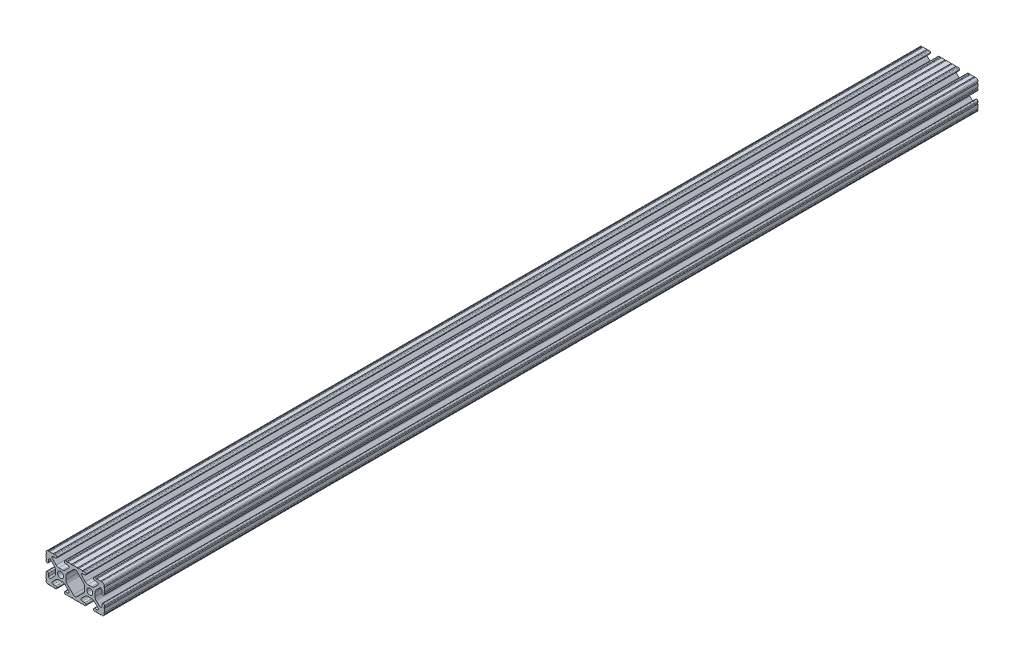
SolidWorks part; units mm, degrees
material "6061 Alloy"
ref_plane "Front Plane" through (0, 0, 0) normal (0, 0, 1) x (1, 0, 0)
ref_plane "Top Plane" through (0, 0, 0) normal (0, 1, 0) x (1, 0, 0)
ref_plane "Right Plane" through (0, 0, 0) normal (1, 0, 0) x (0, 0, -1)
sketch "Sketch1" plane through (0, 0, 0) normal (0, 0, 1) x (1, 0, 0)
  line L0 (-32.9707, 0) -> (32.2708, 0) construction
  line L1 (0, 12.7) -> (0, 0) construction
  line L2 (-12.7, 14.992) -> (-12.7, -12.6999) construction
  line L3 (12.7, 13.9801) -> (12.7, -13.3809) construction
  line L4 (-7.2595, -3.8694) -> (-1.5457, -9.5728)
  line L5 (1.5457, -9.5728) -> (7.2595, -3.8694)
  line L7 (-0.3952, 10.033) -> (0.5515, 10.033)
  line L9 (0.4332, -10.033) -> (-0.4332, -10.033)
  line L12 (8.1915, -1.6223) -> (8.1915, 1.6223)
  line L13 (7.2829, 3.8459) -> (1.6756, 9.5611)
  line L14 (-1.504, 9.5765) -> (-7.252, 3.8768)
  line L15 (-8.1915, 1.6223) -> (-8.1915, -1.6223)
  line L16 (22.2504, 12.7) -> (19.0331, 12.7)
  line L17 (18.0171, 12.7) -> (16.9875, 12.7)
  line L18 (15.9385, 11.651) -> (15.9385, 11.5392)
  line L19 (16.9875, 10.4902) -> (19.1164, 10.4902)
  line L20 (19.8441, 8.7652) -> (16.619, 5.4551)
  line L21 (14.3449, 4.4958) -> (11.0833, 4.4958)
  line L22 (8.817, 5.4472) -> (5.5642, 8.7627)
  line L23 (6.2894, 10.4902) -> (8.4125, 10.4902)
  line L24 (9.4615, 11.5392) -> (9.4615, 11.651)
  line L25 (8.4125, 12.7) -> (7.3829, 12.7)
  line L26 (6.3669, 12.7) -> (3.1496, 12.7)
  line L27 (2.1336, 12.7) -> (-2.1336, 12.7)
  line L28 (-3.1496, 12.7) -> (-6.3669, 12.7)
  line L29 (-7.3829, 12.7) -> (-8.4125, 12.7)
  line L30 (-9.4615, 11.651) -> (-9.4615, 11.5392)
  line L31 (-8.4125, 10.4902) -> (-6.2836, 10.4902)
  line L32 (-5.5326, 8.6661) -> (-8.81, 5.4163)
  line L33 (-11.0455, 4.4958) -> (-14.3545, 4.4958)
  line L34 (-16.59, 5.4163) -> (-19.8674, 8.6661)
  line L35 (-19.1164, 10.4902) -> (-16.9875, 10.4902)
  line L36 (-15.9385, 11.5392) -> (-15.9385, 11.651)
  line L37 (-16.9875, 12.7) -> (-18.0171, 12.7)
  line L38 (-19.0331, 12.7) -> (-22.2504, 12.7)
  line L39 (-25.4, 9.5504) -> (-25.4, 6.3331)
  line L40 (-25.4, 5.3171) -> (-25.4, 4.2375)
  line L41 (-24.401, 3.2385) -> (-24.2392, 3.2385)
  line L42 (-23.1902, 4.2875) -> (-23.1902, 6.3347)
  line L43 (-21.434, 7.0665) -> (-18.148, 3.8082)
  line L44 (-17.2085, 1.5536) -> (-17.2085, -1.6952)
  line L45 (-18.1405, -3.9423) -> (-21.4316, -7.2274)
  line L46 (-23.1902, -6.498) -> (-23.1902, -4.2875)
  line L47 (-24.2392, -3.2385) -> (-24.351, -3.2385)
  line L48 (-25.4, -4.2875) -> (-25.4, -5.3171)
  line L49 (-25.4, -6.3331) -> (-25.4, -9.5504)
  line L50 (-22.2504, -12.7) -> (-19.0331, -12.7)
  line L51 (-18.0171, -12.7) -> (-16.9875, -12.7)
  line L52 (-15.9384, -11.651) -> (-15.9384, -11.5392)
  line L53 (-16.9875, -10.4902) -> (-19.1164, -10.4902)
  line L54 (-19.8341, -8.7551) -> (-16.4966, -5.4237)
  line L55 (-14.2536, -4.4958) -> (-11.1464, -4.4958)
  line L56 (-8.9034, -5.4237) -> (-5.5659, -8.7551)
  line L57 (-6.2836, -10.4902) -> (-8.4125, -10.4902)
  line L58 (-9.4616, -11.5392) -> (-9.4616, -11.651)
  line L59 (-8.4125, -12.7) -> (-7.3829, -12.7)
  line L60 (-6.3669, -12.7) -> (-3.1496, -12.7)
  line L61 (-2.1336, -12.7) -> (2.1336, -12.7)
  line L62 (3.1496, -12.7) -> (6.3669, -12.7)
  line L63 (7.3829, -12.7) -> (8.4125, -12.7)
  line L64 (9.4616, -11.651) -> (9.4616, -11.5392)
  line L65 (8.4125, -10.4902) -> (6.2894, -10.4902)
  line L66 (5.4807, -8.5353) -> (8.5979, -5.4237)
  line L67 (10.8409, -4.4958) -> (14.1026, -4.4958)
  line L68 (16.1879, -5.2766) -> (19.8682, -8.4822)
  line L69 (19.1164, -10.4902) -> (16.9875, -10.4902)
  line L70 (15.9384, -11.5392) -> (15.9384, -11.651)
  line L71 (16.9875, -12.7) -> (18.0171, -12.7)
  line L72 (19.0331, -12.7) -> (22.2504, -12.7)
  line L73 (25.4, -9.5504) -> (25.4, -6.3331)
  line L74 (25.4, -5.3171) -> (25.4, -4.2375)
  line L75 (24.401, -3.2385) -> (24.1892, -3.2385)
  line L76 (23.1902, -4.2375) -> (23.1902, -6.1559)
  line L77 (21.584, -6.8869) -> (18.2982, -4.025)
  line L78 (17.2085, -1.6308) -> (17.2085, 1.6308)
  line L79 (18.1094, 3.8465) -> (21.5263, 7.3534)
  line L80 (23.1902, 6.6769) -> (23.1902, 4.2375)
  line L81 (24.1892, 3.2385) -> (24.401, 3.2385)
  line L82 (25.4, 4.2375) -> (25.4, 5.3171)
  line L83 (25.4, 6.3332) -> (25.4, 9.5504)
  circle A0 centre (-12.7, 0) radius 2.6035
  circle A1 centre (12.7, 0) radius 2.6035
  arc A2 (-0.3952, 10.033) -> (-1.504, 9.5765) centre (-0.3952, 8.4582) ccw
  arc A3 (0.5515, 10.033) -> (1.6756, 9.5611) centre (0.5515, 8.4582) cw
  arc A4 (-8.1915, -1.6223) -> (-7.2595, -3.8694) centre (-5.0165, -1.6223) ccw
  arc A5 (-0.4332, -10.033) -> (-1.5457, -9.5728) centre (-0.4332, -8.4582) cw
  arc A6 (7.2595, -3.8694) -> (8.1915, -1.6223) centre (5.0165, -1.6223) ccw
  arc A7 (8.1915, 1.6223) -> (7.2829, 3.8459) centre (5.0165, 1.6223) ccw
  arc A8 (0.4332, -10.033) -> (1.5457, -9.5728) centre (0.4332, -8.4582) ccw
  arc A9 (-7.252, 3.8768) -> (-8.1915, 1.6223) centre (-5.0165, 1.6223) ccw
  arc A16 (25.3998, 10.5664) -> (23.2664, 12.6998) centre (23.2918, 10.5918) ccw
  arc A17 (22.2504, 12.7) -> (23.2664, 12.6998) centre (22.7584, 12.7) ccw
  arc A18 (18.0171, 12.7) -> (19.0331, 12.7) centre (18.5251, 12.7) ccw
  arc A19 (16.9875, 12.7) -> (15.9385, 11.651) centre (16.9875, 11.651) ccw
  arc A20 (15.9385, 11.5392) -> (16.9875, 10.4902) centre (16.9875, 11.5392) ccw
  arc A21 (19.8441, 8.7652) -> (19.1164, 10.4902) centre (19.1164, 9.4742) ccw
  arc A22 (14.3449, 4.4958) -> (16.619, 5.4551) centre (14.3449, 7.6708) ccw
  arc A23 (8.817, 5.4472) -> (11.0833, 4.4958) centre (11.0833, 7.6708) ccw
  arc A24 (6.2894, 10.4902) -> (5.5642, 8.7627) centre (6.2894, 9.4742) ccw
  arc A25 (8.4125, 10.4902) -> (9.4615, 11.5392) centre (8.4125, 11.5392) ccw
  arc A26 (9.4615, 11.651) -> (8.4125, 12.7) centre (8.4125, 11.651) ccw
  arc A27 (6.3669, 12.7) -> (7.3829, 12.7) centre (6.8749, 12.7) ccw
  arc A28 (2.1336, 12.7) -> (3.1496, 12.7) centre (2.6416, 12.7) ccw
  arc A29 (-3.1496, 12.7) -> (-2.1336, 12.7) centre (-2.6416, 12.7) ccw
  arc A30 (-7.3829, 12.7) -> (-6.3669, 12.7) centre (-6.8749, 12.7) ccw
  arc A31 (-8.4125, 12.7) -> (-9.4615, 11.651) centre (-8.4125, 11.651) ccw
  arc A32 (-9.4615, 11.5392) -> (-8.4125, 10.4902) centre (-8.4125, 11.5392) ccw
  arc A33 (-5.5326, 8.6661) -> (-6.2836, 10.4902) centre (-6.2836, 9.4235) ccw
  arc A34 (-11.0455, 4.4958) -> (-8.81, 5.4163) centre (-11.0455, 7.6708) ccw
  arc A35 (-16.59, 5.4163) -> (-14.3545, 4.4958) centre (-14.3545, 7.6708) ccw
  arc A36 (-19.1164, 10.4902) -> (-19.8674, 8.6661) centre (-19.1164, 9.4235) ccw
  arc A37 (-16.9875, 10.4902) -> (-15.9385, 11.5392) centre (-16.9875, 11.5392) ccw
  arc A38 (-15.9385, 11.651) -> (-16.9875, 12.7) centre (-16.9875, 11.651) ccw
  arc A39 (-19.0331, 12.7) -> (-18.0171, 12.7) centre (-18.5251, 12.7) ccw
  arc A40 (-23.2664, 12.6998) -> (-22.2504, 12.7) centre (-22.7584, 12.7) ccw
  arc A41 (-23.2664, 12.6998) -> (-25.3998, 10.5664) centre (-23.2918, 10.5918) ccw
  arc A42 (-25.4, 9.5504) -> (-25.3998, 10.5664) centre (-25.4, 10.0584) ccw
  arc A43 (-25.4, 5.3171) -> (-25.4, 6.3331) centre (-25.4, 5.8251) ccw
  arc A44 (-25.4, 4.2375) -> (-24.401, 3.2385) centre (-24.401, 4.2375) ccw
  arc A45 (-24.2392, 3.2385) -> (-23.1902, 4.2875) centre (-24.2392, 4.2875) ccw
  arc A46 (-21.434, 7.0665) -> (-23.1902, 6.3347) centre (-22.1596, 6.3347) ccw
  arc A47 (-17.2085, 1.5536) -> (-18.148, 3.8082) centre (-20.3835, 1.5536) ccw
  arc A48 (-18.1405, -3.9423) -> (-17.2085, -1.6952) centre (-20.3835, -1.6952) ccw
  arc A49 (-23.1902, -6.498) -> (-21.4316, -7.2274) centre (-22.1596, -6.498) ccw
  arc A50 (-23.1902, -4.2875) -> (-24.2392, -3.2385) centre (-24.2392, -4.2875) ccw
  arc A51 (-24.351, -3.2385) -> (-25.4, -4.2875) centre (-24.351, -4.2875) ccw
  arc A52 (-25.4, -6.3331) -> (-25.4, -5.3171) centre (-25.4, -5.8251) ccw
  arc A53 (-25.3998, -10.5664) -> (-25.4, -9.5504) centre (-25.4, -10.0584) ccw
  arc A54 (-25.3998, -10.5664) -> (-23.2664, -12.6998) centre (-23.2918, -10.5918) ccw
  arc A55 (-22.2504, -12.7) -> (-23.2664, -12.6998) centre (-22.7584, -12.7) ccw
  arc A56 (-18.0171, -12.7) -> (-19.0331, -12.7) centre (-18.5251, -12.7) ccw
  arc A57 (-16.9875, -12.7) -> (-15.9384, -11.651) centre (-16.9875, -11.651) ccw
  arc A58 (-15.9384, -11.5392) -> (-16.9875, -10.4902) centre (-16.9875, -11.5392) ccw
  arc A59 (-19.8341, -8.7551) -> (-19.1164, -10.4902) centre (-19.1164, -9.4742) ccw
  arc A60 (-14.2536, -4.4958) -> (-16.4966, -5.4237) centre (-14.2536, -7.6708) ccw
  arc A61 (-8.9034, -5.4237) -> (-11.1464, -4.4958) centre (-11.1464, -7.6708) ccw
  arc A62 (-6.2836, -10.4902) -> (-5.5659, -8.7551) centre (-6.2836, -9.4742) ccw
  arc A63 (-8.4125, -10.4902) -> (-9.4616, -11.5392) centre (-8.4125, -11.5392) ccw
  arc A64 (-9.4616, -11.651) -> (-8.4125, -12.7) centre (-8.4125, -11.651) ccw
  arc A65 (-6.3669, -12.7) -> (-7.3829, -12.7) centre (-6.8749, -12.7) ccw
  arc A66 (-2.1336, -12.7) -> (-3.1496, -12.7) centre (-2.6416, -12.7) ccw
  arc A67 (3.1496, -12.7) -> (2.1336, -12.7) centre (2.6416, -12.7) ccw
  arc A68 (7.3829, -12.7) -> (6.3669, -12.7) centre (6.8749, -12.7) ccw
  arc A69 (8.4125, -12.7) -> (9.4616, -11.651) centre (8.4125, -11.651) ccw
  arc A70 (9.4616, -11.5392) -> (8.4125, -10.4902) centre (8.4125, -11.5392) ccw
  arc A71 (5.4807, -8.5353) -> (6.2894, -10.4902) centre (6.2894, -9.3455) ccw
  arc A72 (10.8409, -4.4958) -> (8.5979, -5.4237) centre (10.8409, -7.6708) ccw
  arc A73 (16.1879, -5.2766) -> (14.1026, -4.4958) centre (14.1026, -7.6708) ccw
  arc A74 (19.1164, -10.4902) -> (19.8682, -8.4822) centre (19.1164, -9.3455) ccw
  arc A75 (16.9875, -10.4902) -> (15.9384, -11.5392) centre (16.9875, -11.5392) ccw
  arc A76 (15.9384, -11.651) -> (16.9875, -12.7) centre (16.9875, -11.651) ccw
  arc A77 (19.0331, -12.7) -> (18.0171, -12.7) centre (18.5251, -12.7) ccw
  arc A78 (23.2664, -12.6998) -> (22.2504, -12.7) centre (22.7584, -12.7) ccw
  arc A79 (23.2664, -12.6998) -> (25.3998, -10.5664) centre (23.2918, -10.5918) ccw
  arc A80 (25.4, -9.5504) -> (25.3998, -10.5664) centre (25.4, -10.0584) ccw
  arc A81 (25.4, -5.3171) -> (25.4, -6.3331) centre (25.4, -5.8251) ccw
  arc A82 (25.4, -4.2375) -> (24.401, -3.2385) centre (24.401, -4.2375) ccw
  arc A83 (24.1892, -3.2385) -> (23.1902, -4.2375) centre (24.1892, -4.2375) ccw
  arc A84 (21.584, -6.8869) -> (23.1902, -6.1559) centre (22.2207, -6.1559) ccw
  arc A85 (17.2085, -1.6308) -> (18.2982, -4.025) centre (20.3835, -1.6308) ccw
  arc A86 (18.1094, 3.8465) -> (17.2085, 1.6308) centre (20.3835, 1.6308) ccw
  arc A87 (23.1902, 6.6769) -> (21.5263, 7.3534) centre (22.2207, 6.6769) ccw
  arc A88 (23.1902, 4.2375) -> (24.1892, 3.2385) centre (24.1892, 4.2375) ccw
  arc A89 (24.401, 3.2385) -> (25.4, 4.2375) centre (24.401, 4.2375) ccw
  arc A90 (25.4, 6.3332) -> (25.4, 5.3171) centre (25.4, 5.8251) ccw
  arc A91 (25.3998, 10.5664) -> (25.4, 9.5504) centre (25.4, 10.0584) ccw
  dimension "D1" = 5.207
  dimension "D6" = 6.477
  dimension "D7" = 14.859
  dimension "D14" = 1.5748
  dimension "D16" = 1.5748
  dimension "D15" = 3.175
  dimension "D2" = 25.4
  dimension "D3" = 50.8
  dimension "D4" = 25.4
  dimension "D5" = 8.2042
  dimension "D8" = 2.2098
  dimension "D9" = 2.2098
  dimension "D10" = 2.2098
  dimension "D11" = 2.2098
  dimension "D12" = 2.2098
  dimension "D13" = 6.477
extrude "Extrude1" add sketch "Sketch1" against normal blind 760.984
